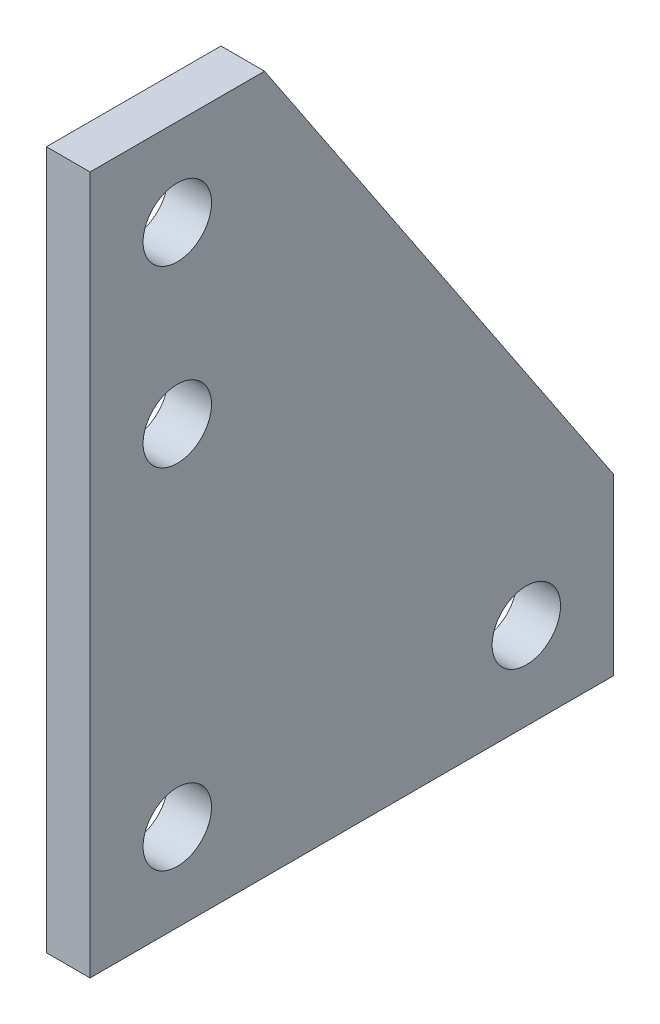
SolidWorks part; units mm, degrees
ref_plane "Front Plane" through (0, 0, 0) normal (0, 0, 1) x (1, 0, 0)
ref_plane "Top Plane" through (0, 0, 0) normal (0, 1, 0) x (1, 0, 0)
ref_plane "Right Plane" through (0, 0, 0) normal (1, 0, 0) x (0, 0, -1)
sketch "Sketch3" plane through (0, 0, 0) normal (1, 0, 0) x (0, 0, -1)
  line L0 (0, 0) -> (38.1, 0)
  line L1 (38.1, 0) -> (38.1, 12.7)
  line L4 (0, 50.8) -> (0, 0)
  line L5 (0, 50.8) -> (12.7, 50.8)
  line L6 (12.7, 50.8) -> (38.1, 12.7)
  circle A0 centre (6.35, 44.45) radius 2.4892
  circle A1 centre (6.35, 31.75) radius 2.4892
  circle A2 centre (6.35, 6.35) radius 2.4892
  circle A3 centre (31.75, 6.35) radius 2.4892
  point P15 (38.1, 6.35)
  dimension "D5" = 12.7
  dimension "D9" = 4.9784
  dimension "D1" = 50.8
  dimension "D2" = 6.35
  dimension "D3" = 38.1
  dimension "D4" = 12.7
  dimension "D6" = 12.7
  dimension "D7" = 25.4
  dimension "D8" = 6.35
extrude "Boss-Extrude1" add sketch "Sketch3" along normal blind 3.175
equation "\"Thick\"= \"in\""
